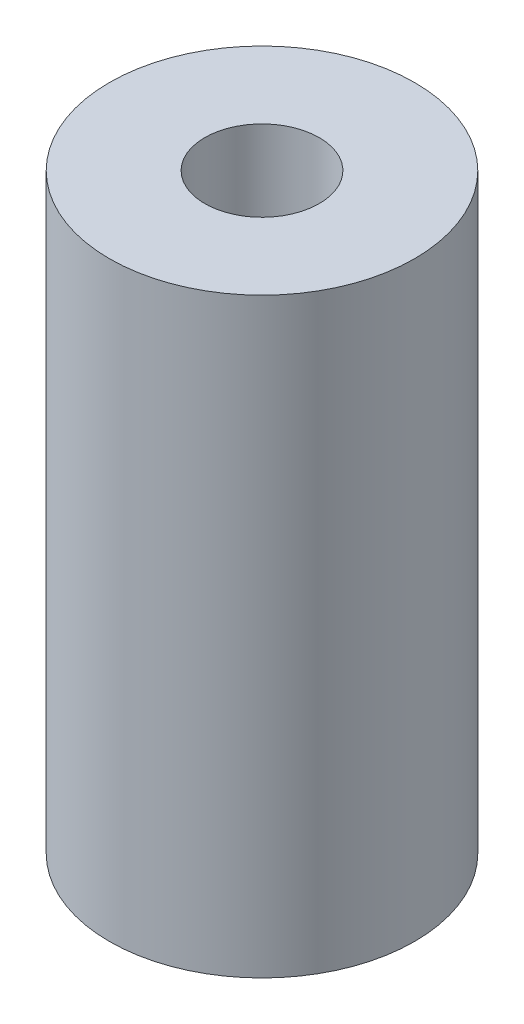
SolidWorks part; units mm, degrees
ref_plane "Спереди" through (0, 0, 0) normal (0, 0, 1) x (1, 0, 0)
ref_plane "Сверху" through (0, 0, 0) normal (0, 1, 0) x (1, 0, 0)
ref_plane "Справа" through (0, 0, 0) normal (1, 0, 0) x (0, 0, -1)
sketch "Эскиз1" plane through (0, 0, 0) normal (0, 0, 1) x (1, 0, 0)
  line L0 (0, 0) -> (0, 15.5366) construction
  line L1 (1.5, 15.5366) -> (4, 15.5366)
  line L2 (4, 15.5366) -> (4, 0.0366)
  line L3 (4, 0.0366) -> (1.5, 0.0366)
  line L4 (1.5, 0.0366) -> (1.5, 15.5366)
  dimension "D1" = 1.5
  dimension "D2" = 4
  dimension "D3" = 15.5
revolve "Повернуть1" add sketch "Эскиз1" angle 360 about L0
